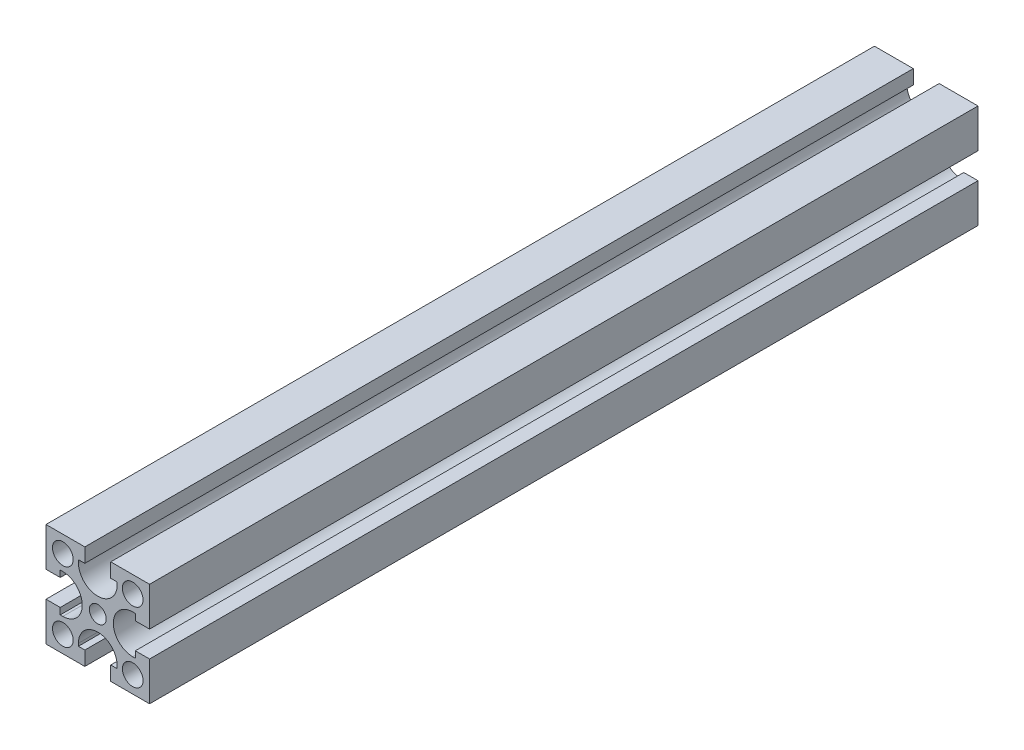
SolidWorks part; units mm, degrees
ref_plane "前基準面" through (0, 0, 0) normal (0, 0, 1) x (1, 0, 0)
ref_plane "上基準面" through (0, 0, 0) normal (0, 1, 0) x (1, 0, 0)
ref_plane "右基準面" through (0, 0, 0) normal (1, 0, 0) x (0, 0, -1)
sketch "草圖1" plane through (0, 0, 0) normal (0, 0, 1) x (1, 0, 0)
  line L0 (0, 20) -> (0, -20) construction
  line L1 (-20, -20) -> (20, -20)
  line L2 (-20, -20) -> (-20, 20)
  line L3 (-20, 20) -> (20, 20)
  line L4 (20, -20) -> (20, 20)
  dimension "D1" = 40
  dimension "D2" = 40
extrude "伸長1" add sketch "草圖1" along normal blind 320
sketch "草圖2" plane through (0, 0, 0) normal (0, 0, -1) x (-1, 0, 0)
  line L0 (-20, 20) -> (20, 20) construction
  line L4 (5, 14.5) -> (7.5, 14.5)
  line L5 (14.5, -5) -> (14.5, -7.5)
  line L6 (-5, 14.5) -> (-5, 20)
  line L7 (-5, 20) -> (5, 20)
  line L8 (5, 14.5) -> (5, 20)
  line L9 (14.5, 5) -> (20, 5)
  line L10 (-7.5, 13.5) -> (-7.5, 14.5)
  line L11 (-7.5, 14.5) -> (-5, 14.5)
  line L12 (7.5, 13.5) -> (7.5, 14.5)
  line L13 (20, 5) -> (20, -5)
  line L14 (14.5, -5) -> (20, -5)
  line L15 (13.5, 7.5) -> (14.5, 7.5)
  line L16 (14.5, 7.5) -> (14.5, 5)
  line L17 (13.5, -7.5) -> (14.5, -7.5)
  line L18 (-5, -14.5) -> (-7.5, -14.5)
  line L19 (5, -14.5) -> (5, -20)
  line L20 (5, -20) -> (-5, -20)
  line L21 (-5, -14.5) -> (-5, -20)
  line L22 (7.5, -13.5) -> (7.5, -14.5)
  line L23 (7.5, -14.5) -> (5, -14.5)
  line L24 (-7.5, -13.5) -> (-7.5, -14.5)
  line L25 (-14.5, 5) -> (-14.5, 7.5)
  line L26 (-14.5, -5) -> (-20, -5)
  line L27 (-20, -5) -> (-20, 5)
  line L28 (-14.5, 5) -> (-20, 5)
  line L29 (-13.5, -7.5) -> (-14.5, -7.5)
  line L30 (-14.5, -7.5) -> (-14.5, -5)
  line L31 (-13.5, 7.5) -> (-14.5, 7.5)
  line L32 (0, -20) -> (0, 0) construction
  line L33 (20, -20) -> (-20, -20) construction
  line L34 (0, 0) -> (-20, 0) construction
  line L35 (-20, -20) -> (-20, 20) construction
  line L36 (20, 20) -> (20, -20) construction
  circle A0 centre (0, 0) radius 3.25
  circle A1 centre (-13.5, 13.5) radius 4
  circle A2 centre (13.5, 13.5) radius 4
  circle A3 centre (-13.5, -13.5) radius 4
  circle A4 centre (13.5, -13.5) radius 4
  arc A5 (-7.5, 13.5) -> (7.5, 13.5) centre (0, 13.5) ccw
  arc A6 (13.5, 7.5) -> (13.5, -7.5) centre (13.5, 0) ccw
  arc A7 (7.5, -13.5) -> (-7.5, -13.5) centre (0, -13.5) ccw
  arc A8 (-13.5, -7.5) -> (-13.5, 7.5) centre (-13.5, 0) ccw
  dimension "D1" = 6.5
  dimension "D2" = 8
  dimension "D5" = 15
  dimension "D12" = 5.5
  dimension "D3" = 27
  dimension "D4" = 27
  dimension "D6" = 10
extrude "除料-伸長1" cut sketch "草圖2" against normal through all
hole_wizard "Ø3.5 (3.5) 直徑孔1" positions "草圖7" profile "草圖6" hole size "Ø3.5" standard "JIS"
sketch "草圖7" plane through (0, -20, 0) normal (0, -1, 0) x (-1, 0, 0)
  line L0 (-5, 0) -> (-20, 0) construction
  line L1 (-20, -320) -> (-20, 0) construction
  line L5 (20, -160) -> (-20, -160) construction
  line L6 (20, -320) -> (20, 0) construction
  line L11 (-1, -180.7177) -> (-1, -138.9378) construction
  point P0 (-16, -145)
  point P28 (-16, -175)
  point P37 (14, -145)
  point P38 (14, -175)
  dimension "D1" = 145
  dimension "D2" = 4
  dimension "D3" = 15
  dimension "D4" = 15
sketch "草圖6" plane through (16, -20, 145) normal (1, 0, 0) x (0, 0, -1)
  line L0 (0, 0) -> (0, 8.5515)
  line L1 (0, 8.5515) -> (1.75, 7.5)
  line L2 (1.75, 7.5) -> (1.75, 0)
  line L5 (1.75, 0) -> (0, 0)
  line L10 (0, 8.5515) -> (-1.75, 7.5) construction
  line L11 (0, -6.35) -> (0, 107.95) construction
  dimension "鑽孔直徑" = 3.5
  dimension "鑽孔深度" = 7.5
  dimension "導頭角度" = 118
